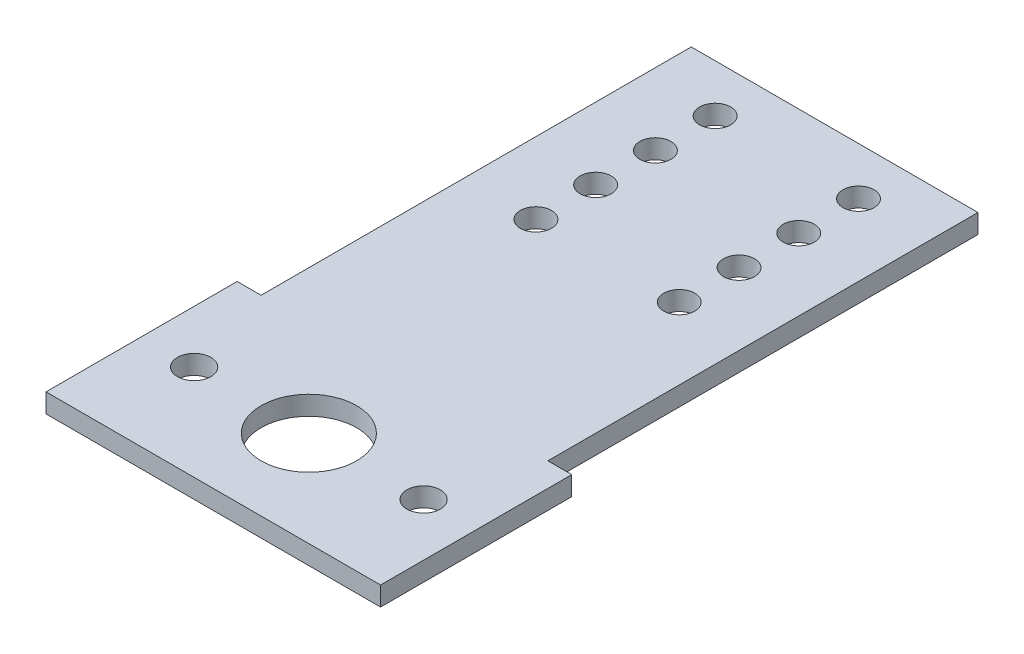
SolidWorks part; units mm, degrees
ref_plane "Front Plane" through (0, 0, 0) normal (0, 0, 1) x (1, 0, 0)
ref_plane "Top Plane" through (0, 0, 0) normal (0, 1, 0) x (1, 0, 0)
ref_plane "Right Plane" through (0, 0, 0) normal (1, 0, 0) x (0, 0, -1)
sketch "Sketch1" plane through (0, 0, 0) normal (0, 1, 0) x (1, 0, 0)
  line L1 (-30, 65) -> (30, 65)
  line L2 (-30, 65) -> (-30, -65)
  line L3 (-30, -65) -> (30, -65)
  line L4 (30, 65) -> (30, -65)
  line L5 (0, -65) -> (0, 65) construction
  line L6 (-30, 0) -> (30, 0) construction
  point P0 (0, 0)
  dimension "D1" = 60
  dimension "D2" = 130
extrude "Boss-Extrude1" add sketch "Sketch1" along normal blind 4
sketch "Sketch2" plane through (0, 0, 0) normal (0, 1, 0) x (1, 0, 0)
  line L0 (-35, -25) -> (-35, -65)
  line L1 (-35, -25) -> (35, -25)
  line L2 (-35, -65) -> (35, -65)
  line L3 (35, -25) -> (35, -65)
  line L4 (0, -65) -> (0, -25) construction
  line L5 (-35, -45) -> (35, -45) construction
  line L6 (0, 0) -> (0, -21.055) construction
  point P1 (0, -45)
  dimension "D1" = 70
  dimension "D2" = 40
extrude "Boss-Extrude2" add sketch "Sketch2" along normal blind 4
sketch "Sketch3" plane through (0, 4, 0) normal (0, 1, 0) x (1, 0, 0)
  line L0 (0, 0) -> (0, -65) construction
  line L1 (-35, -65) -> (35, -65) construction
  line L2 (-24, -45) -> (24, -45)
  circle A0 centre (24, -45) radius 3.5
  circle A1 centre (-24, -45) radius 3.5
  circle A2 centre (0, -45) radius 10
  point P8 (0, -45)
  dimension "D1" = 7
  dimension "D4" = 20
  dimension "D2" = 48
  dimension "D3" = 20
extrude "Cut-Extrude1" cut sketch "Sketch3" against normal through all contours A1 | A2 | A0
sketch "Sketch4" plane through (0, 4, 0) normal (0, 1, 0) x (1, 0, 0)
  line L0 (0, 0) -> (0, 65) construction
  line L1 (30, 65) -> (-30, 65) construction
  line L2 (-15, 55) -> (15, 55) construction
  circle A0 centre (15, 55) radius 3.25
  circle A1 centre (-15, 55) radius 3.25
  point P8 (0, 55)
  dimension "D1" = 6.5
  dimension "D2" = 30
  dimension "D3" = 10
extrude "Cut-Extrude2" cut sketch "Sketch4" against normal through all and the other way through all
pattern_linear "LPattern1" count 4 spacing 12.5 along (0, 0, 1) of "Cut-Extrude2"
